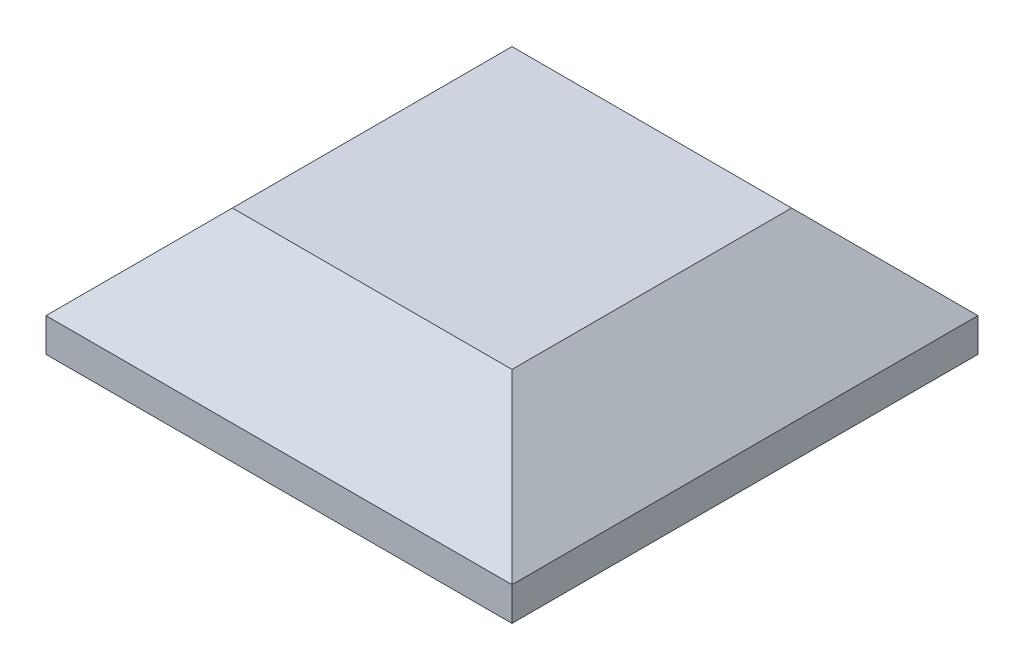
SolidWorks part; units mm, degrees
ref_plane "Front Plane" through (0, 0, 0) normal (0, 0, 1) x (1, 0, 0)
ref_plane "Top Plane" through (0, 0, 0) normal (0, 1, 0) x (1, 0, 0)
ref_plane "Right Plane" through (0, 0, 0) normal (1, 0, 0) x (0, 0, -1)
sketch "Sketch1" plane through (0, 0, 0) normal (0, 1, 0) x (1, 0, 0)
  line L1 (0.715, -5.0318) -> (-11.785, -5.0318)
  line L2 (0.715, -5.0318) -> (0.715, 7.4682)
  line L3 (0.715, 7.4682) -> (-11.785, 7.4682)
  line L4 (-11.785, -5.0318) -> (-11.785, 7.4682)
  dimension "D1" = 12.5
  dimension "D2" = 12.5
extrude "Boss-Extrude1" add sketch "Sketch1" along normal blind 3.4
chamfer "Chamfer2" distance 2.5 angle 45 4 edges at (-5.535, 3.4, 5.0318) (-11.785, 3.4, -1.2182) (-5.535, 3.4, -7.4682) (0.715, 3.4, -1.2182)
